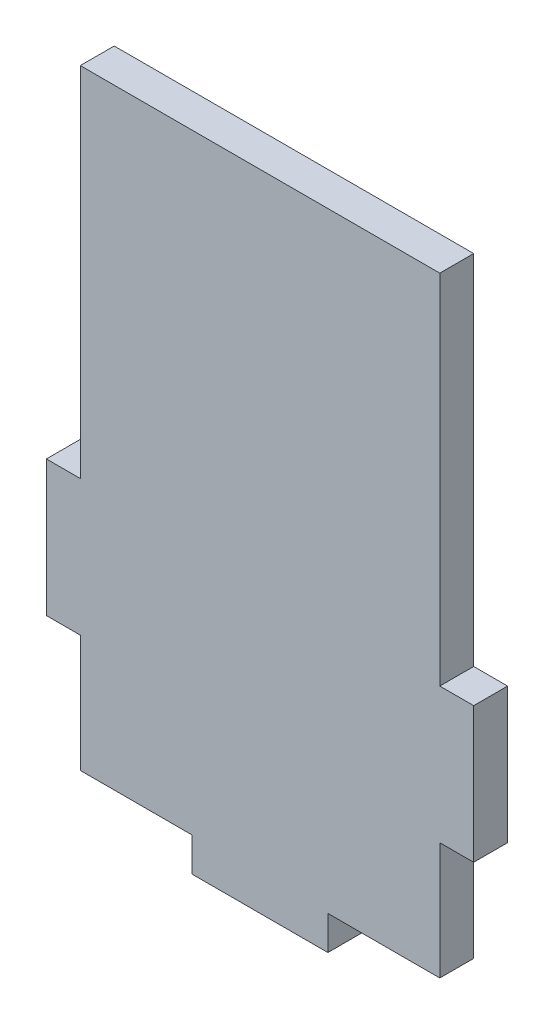
SolidWorks part; units mm, degrees
ref_plane "Front Plane" through (0, 0, 0) normal (0, 0, 1) x (1, 0, 0)
ref_plane "Top Plane" through (0, 0, 0) normal (0, 1, 0) x (1, 0, 0)
ref_plane "Right Plane" through (0, 0, 0) normal (1, 0, 0) x (0, 0, -1)
sketch "Sketch1" plane through (0, 0, 0) normal (0, 0, 1) x (1, 0, 0)
  line L0 (0, -45) -> (0, -50) construction
  line L1 (-26.5, 45) -> (26.5, 45)
  line L2 (-26.5, 45) -> (-26.5, -7.7249)
  line L3 (-26.5, -45) -> (-10.0464, -45)
  line L4 (26.5, 45) -> (26.5, -7.7249)
  line L5 (-26.5, 45) -> (26.5, -45) construction
  line L6 (-26.5, -45) -> (26.5, 45) construction
  line L7 (-5.5, -50) -> (31, -50) construction
  line L8 (10, -50) -> (-10, -50)
  line L9 (-11.5, -50) -> (31, -50) construction
  line L10 (-10, -50) -> (-10.0464, -45)
  line L11 (10, -50) -> (10, -45)
  line L12 (10, -45) -> (26.5, -45)
  line L13 (-30.5, 9.1309) -> (-21.8243, 9.1309) construction
  line L14 (-29.5, 9.1309) -> (-31.5, 9.1309) construction
  line L15 (-21.8243, 9.1309) -> (-21.8243, -45) construction
  line L16 (-26.5, -17.7249) -> (-31.5, -17.7249) construction
  line L17 (0, 0) -> (0, 15.0384) construction
  line L18 (-31.5, -7.7249) -> (-31.5, -27.7249)
  line L19 (-31.5, 212.5) -> (-31.5, -115) construction
  line L20 (-31.5, -7.7249) -> (-26.5, -7.7249)
  line L21 (-31.5, -27.7249) -> (-26.5, -27.7249)
  line L22 (-26.5, -27.7249) -> (-26.5, -45)
  line L23 (-31.5, -7.7249) -> (-26.5, -7.7249)
  line L24 (-31.5, -27.7249) -> (-26.5, -27.7249)
  line L25 (26.5, -17.7249) -> (31.5, -17.7249) construction
  line L26 (31.5, -27.7249) -> (26.5, -27.7249)
  line L27 (31.5, -7.7249) -> (26.5, -7.7249)
  line L28 (31.5, -27.7249) -> (26.5, -27.7249)
  line L29 (31.5, -7.7249) -> (26.5, -7.7249)
  line L30 (31.5, -7.7249) -> (31.5, -27.7249)
  line L31 (26.5, -27.7249) -> (26.5, -45)
  point P0 (0, 0)
  point P15 (0, -50)
  point P32 (-31.5, -17.7249)
  point P40 (31.5, -17.7249)
  dimension "D1" = 90
  dimension "D2" = 53
  dimension "D3" = 20
  dimension "D4" = 5
  dimension "D5" = 20
extrude "Boss-Extrude1" add sketch "Sketch1" along normal blind 5 contours L31 L26 L30 L27 L4 L1 L2 L20 L18 L21 L22 L3 L10 L8 L11 L12
